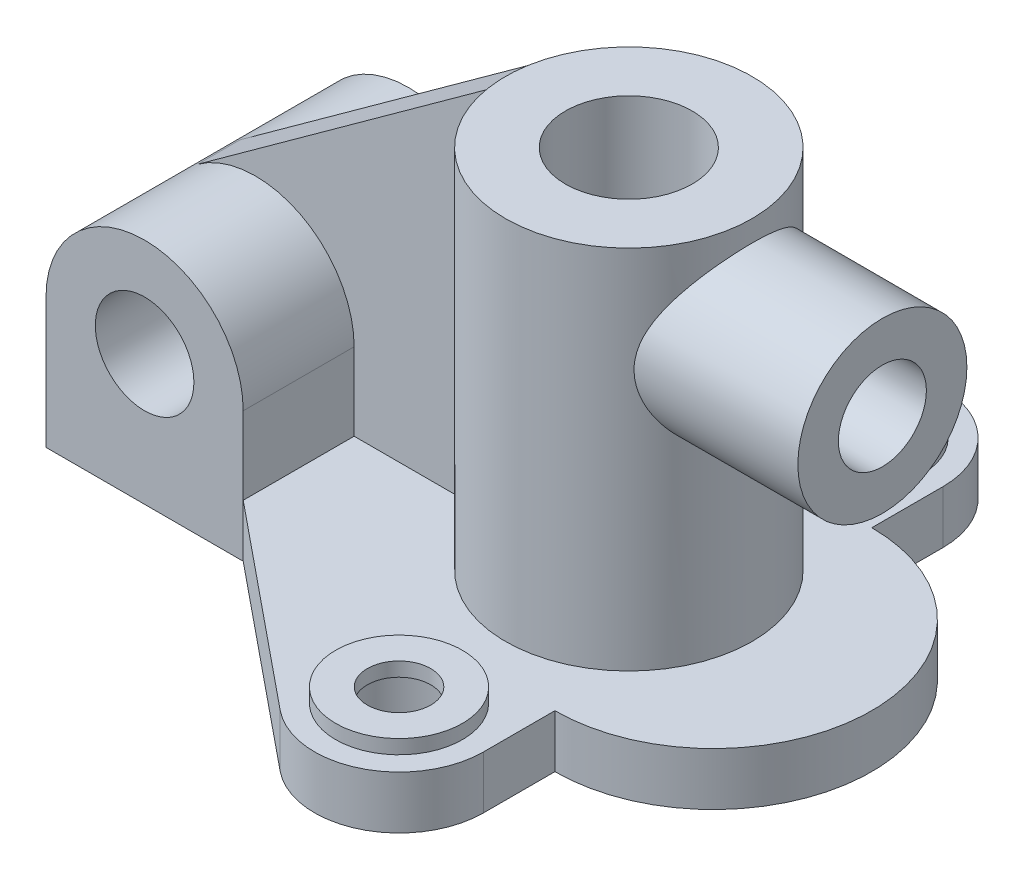
SolidWorks part; units mm, degrees
ref_plane "Front Plane" through (0, 0, 0) normal (0, 0, 1) x (1, 0, 0)
ref_plane "Top Plane" through (0, 0, 0) normal (0, 1, 0) x (1, 0, 0)
ref_plane "Right Plane" through (0, 0, 0) normal (1, 0, 0) x (0, 0, -1)
sketch "Sketch1" plane through (0, 0, 0) normal (0, 1, 0) x (1, 0, 0)
  line L0 (-269.0851, 0) -> (141.2067, 0) construction
  line L1 (0, -45) -> (0, -65.2491)
  line L2 (0, 45) -> (0, 65.2491)
  line L3 (-39.1682, 83.8482) -> (-96, 37.5)
  line L4 (-96, 37.5) -> (-152, 37.5)
  line L5 (-152, 37.5) -> (-152, -37.5)
  line L6 (-96, -37.5) -> (-152, -37.5)
  line L7 (-39.1682, -83.8482) -> (-96, -37.5)
  arc A0 (0, -45) -> (0, 45) centre (0, 0) ccw
  arc A1 (0, 65.2491) -> (-39.1682, 83.8482) centre (-24, 65.2491) ccw
  arc A2 (0, -65.2491) -> (-39.1682, -83.8482) centre (-24, -65.2491) cw
  circle A3 centre (-24, 65.2491) radius 18
  circle A4 centre (-24, -65.2491) radius 18
  point P18 (-152, 0)
  dimension "D1" = 45
  dimension "D2" = 24
  dimension "D6" = 36
  dimension "D7" = 36
  dimension "D3" = 75
  dimension "D4" = 56
  dimension "D5" = 128
extrude "Boss-Extrude1" add sketch "Sketch1" along normal blind 15
sketch "Sketch2" plane through (0, 15, 0) normal (0, 1, 0) x (1, 0, 0)
  circle A0 centre (-24, 65.2491) radius 9
  circle A2 centre (-24, 65.2491) radius 18
  circle A4 centre (-24, -65.2491) radius 9
  circle A5 centre (-24, -65.2491) radius 18
  dimension "D1" = 36
  dimension "D2" = 18
  dimension "D3" = 36
  dimension "D4" = 18
extrude "Boss-Extrude2" add sketch "Sketch2" along normal blind 4
sketch "Sketch3" plane through (0, 15, 0) normal (0, 1, 0) x (1, 0, 0)
  line L0 (-24, 74.2491) -> (-24, -101.1892) construction
  circle A2 centre (-24, 65.2491) radius 9 construction
  circle A3 centre (-24, 0) radius 18
  circle A4 centre (-24, 0) radius 35
  dimension "D1" = 70
  dimension "D2" = 36
extrude "Boss-Extrude3" add sketch "Sketch3" along normal blind 104
sketch "Sketch4" plane through (0, 0, 37.5) normal (0, 0, 1) x (1, 0, 0)
  line L0 (-152, 15) -> (-152, 37)
  line L1 (-96, 15) -> (-96, 37)
  arc A0 (-96, 37) -> (-152, 37) centre (-124, 37) ccw
  circle A1 centre (-124, 37) radius 14
  point P8 (0, 0)
  point P9 (-96, 35)
  point P10 (0, 0)
  line M6 (-96, 15) -> (-152, 15)
  dimension "D1" = 28
  dimension "D2" = 22
  dimension "56" = 28
extrude "Boss-Extrude4" add sketch "Sketch4" against normal blind 75 contours L1 A0 L0 A1 M6
ref_plane "Plane1" through (-24, 0, 0) normal (1, 0, 0) x (0, 0, -1)
sketch "Sketch6" plane through (-24, 0, 0) normal (1, 0, 0) x (0, 0, -1)
  circle A0 centre (0, 89) radius 12.5
  circle A1 centre (0, 89) radius 24
  point P3 (0, 0)
  dimension "D2" = 48
  dimension "D3" = 25
  dimension "D1" = 89
extrude "Boss-Extrude5" add sketch "Sketch6" along normal blind 72
sketch "Sketch8" plane through (0, 119, 0) normal (0, 1, 0) x (1, 0, 0)
  circle A1 centre (-24, 0) radius 35
  circle A2 centre (-24, 0) radius 35
  dimension "D1" = 0
sketch "Sketch9" plane through (0, 119, 0) normal (0, 1, 0) x (1, 0, 0)
  circle A0 centre (-24, 0) radius 18
extrude "Cut-Extrude2" cut sketch "Sketch9" against normal through all
sketch "Sketch17" plane through (0, 0, 0) normal (0, 0, 1) x (1, 0, 0)
  line L0 (-59, 118.582) -> (-139.2585, 60.5203)
  line L1 (-59, 119) -> (-59, 15) construction
  arc A2 (-96, 37) -> (-152, 37) centre (-124, 37) ccw construction
  point P4 (0, 0)
  point P5 (0, 0)
  point P7 (0, 0)
  point P8 (0, 0)
  point P11 (0, 0)
  point P12 (0, 0)
  point P15 (-59, 118.582)
rib "Rib1" sketch "Sketch17" sketch "Sketch17" thickness 12 extrusion direction parallel to sketch draft on no parameters "D1"=12
